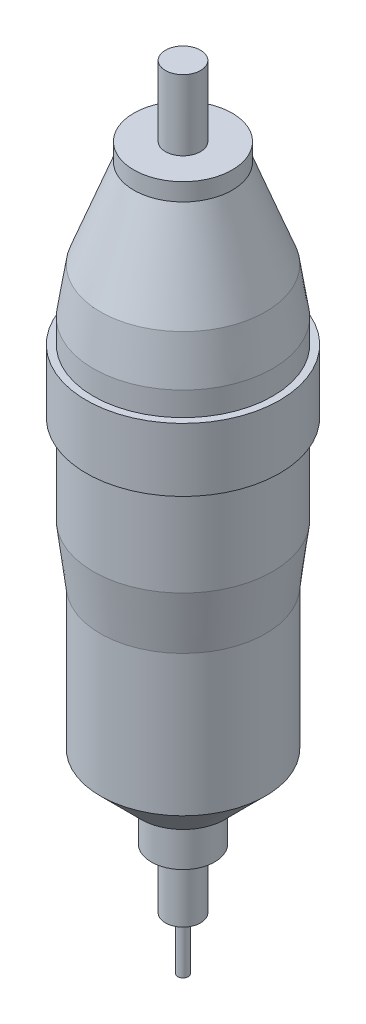
SolidWorks part; units mm, degrees
material "Plain Carbon Steel"
ref_plane "Front Plane" through (0, 0, 0) normal (0, 0, 1) x (1, 0, 0)
ref_plane "Top Plane" through (0, 0, 0) normal (0, 1, 0) x (1, 0, 0)
ref_plane "Right Plane" through (0, 0, 0) normal (1, 0, 0) x (0, 0, -1)
sketch "Sketch1" plane through (0, 0, 0) normal (0, 0, 1) x (1, 0, 0)
  line L0 (0, 86.1006) -> (0, -103.8994) construction
  line L1 (0, 86.1006) -> (14, 86.1006)
  line L2 (14, 86.1006) -> (14, 81.1006)
  line L3 (14, 81.1006) -> (23.5, 55.8893)
  line L4 (23.5, 55.8893) -> (25.5, 42.8893)
  line L5 (25.5, 42.8893) -> (25.5, 36.1006)
  line L6 (25.5, -7.1107) -> (23.5, -23.3994)
  line L7 (23.5, -23.3994) -> (23.5, -63.3994)
  line L8 (23.5, -63.3994) -> (12, -74.8994)
  line L9 (12, -74.8994) -> (9, -74.8994)
  line L10 (9, -74.8994) -> (9, -86.8994)
  line L11 (9, -86.8994) -> (5, -86.8994)
  line L12 (25.5, 18.1006) -> (27.5, 18.1006)
  line L13 (27.5, 18.1006) -> (27.5, 36.1006)
  line L14 (27.5, 36.1006) -> (25.5, 36.1006)
  line L15 (25.5, 18.1006) -> (25.5, -7.1107)
  line L16 (0, -103.8994) -> (5, -103.8994)
  line L17 (5, -86.8994) -> (5, -103.8994)
  line L18 (0, 86.1006) -> (0, -103.8994)
  dimension "D1" = 5
  dimension "D2" = 40
  dimension "D3" = 12
  dimension "D4" = 122
  dimension "D5" = 9
  dimension "D6" = 23.5
  dimension "D7" = 45
  dimension "D8" = 25.5
  dimension "D9" = 14
  dimension "D10" = 5
  dimension "D11" = 17
  dimension "D12" = 2
  dimension "D13" = 18
  dimension "D14" = 50
  dimension "D15" = 7
  dimension "D16" = 13
  dimension "D17" = 190
  dimension "D18" = 3
revolve "Revolve1" add sketch "Sketch1" angle 360 about L0
sketch "Sketch2" plane through (0, 86.1006, 0) normal (0, 1, 0) x (1, 0, 0)
  circle A0 centre (0, 0) radius 5
extrude "Extrude1" add sketch "Sketch2" along normal blind 20
sketch "Sketch3" plane through (0, -103.8994, 0) normal (0, -1, 0) x (1, 0, 0)
  circle A0 centre (0, 0) radius 1.5
extrude "Extrude2" add sketch "Sketch3" along normal blind 15
ref_point "Point1"
sketch "Sketch4" plane through (0, -118.8994, 0) normal (0, -1, 0) x (1, 0, 0)
  line L1 (0, 41.6863) -> (0, -43.2622) construction
ref_plane "Plane1" through (27.5, 0, 0) normal (1, 0, 0) x (0, 0, -1)
